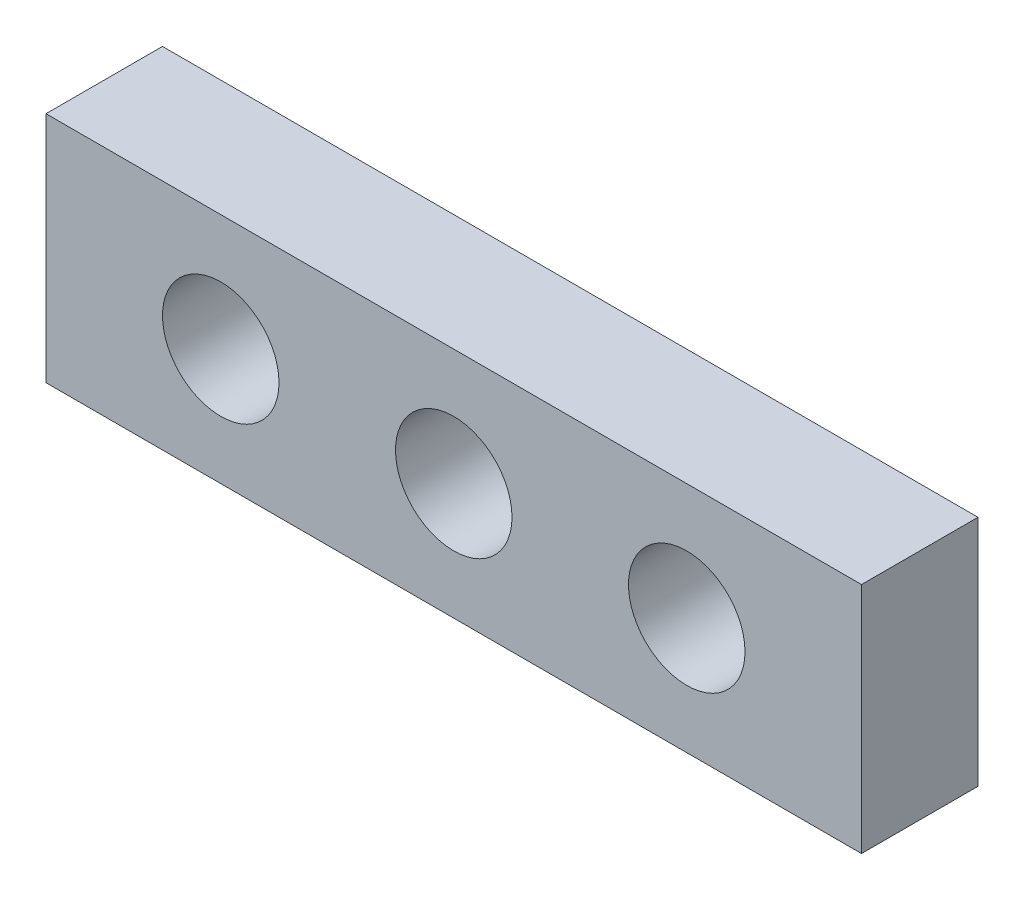
SolidWorks part; units mm, degrees
ref_plane "Front Plane" through (0, 0, 0) normal (0, 0, 1) x (1, 0, 0)
ref_plane "Top Plane" through (0, 0, 0) normal (0, 1, 0) x (1, 0, 0)
ref_plane "Right Plane" through (0, 0, 0) normal (1, 0, 0) x (0, 0, -1)
sketch "Sketch1" plane through (0, 0, 0) normal (0, 0, 1) x (1, 0, 0)
  line L1 (0, 0) -> (140, 0)
  line L2 (0, 0) -> (0, 40)
  line L3 (0, 40) -> (140, 40)
  line L4 (140, 0) -> (140, 40)
  circle A0 centre (30, 20) radius 10
  circle A1 centre (70, 20) radius 10
  circle A2 centre (110, 20) radius 10
  dimension "D3" = 20
  dimension "D1" = 140
  dimension "D2" = 40
  dimension "D4" = 30
  dimension "D5" = 20
  dimension "D7" = 40
  dimension "D6" = 3
extrude "Boss-Extrude1" add sketch "Sketch1" against normal blind 20
